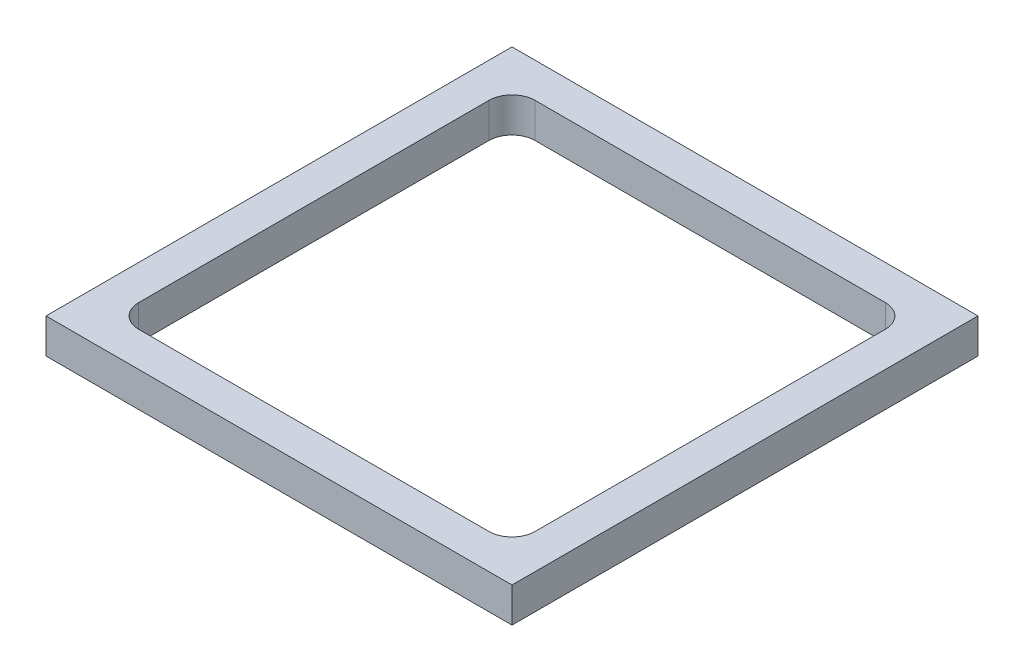
SolidWorks part; units mm, degrees
material "6061-T6 (SS)"
ref_plane "Front Plane" through (0, 0, 0) normal (0, 0, 1) x (1, 0, 0)
ref_plane "Top Plane" through (0, 0, 0) normal (0, 1, 0) x (1, 0, 0)
ref_plane "Right Plane" through (0, 0, 0) normal (1, 0, 0) x (0, 0, -1)
sketch "Sketch1" plane through (0, 0, 0) normal (0, 1, 0) x (1, 0, 0)
  line L5 (0, 0) -> (127.635, 0)
  line L6 (0, 0) -> (0, 127.635)
  line L7 (0, 127.635) -> (127.635, 127.635)
  line L8 (127.635, 0) -> (127.635, 127.635)
  dimension "D1" = 127.635
  dimension "D2" = 127.635
extrude "Boss-Extrude1" add sketch "Sketch1" along normal blind 9.525 contours L5 L8 L7 L6
sketch "Sketch5" plane through (0, 9.525, 0) normal (0, 1, 0) x (1, 0, 0)
  line L0 (63.8175, 127.635) -> (63.8175, 0) construction
  line L1 (0, 127.635) -> (127.635, 127.635) construction
  line L2 (0, 0) -> (127.635, 0) construction
  line L4 (9.525, 118.11) -> (118.11, 118.11)
  line L5 (9.525, 118.11) -> (9.525, 9.525)
  line L6 (9.525, 9.525) -> (118.11, 9.525)
  line L7 (118.11, 118.11) -> (118.11, 9.525)
  line L8 (9.525, 118.11) -> (118.11, 9.525) construction
  line L9 (9.525, 9.525) -> (118.11, 118.11) construction
  point P6 (63.8175, 63.8175)
  dimension "D1" = 108.585
  dimension "D2" = 108.585
extrude "Cut-Extrude1" cut sketch "Sketch5" against normal blind 9.525 contours L5 L4 L7 L6
fillet "Fillet1" radius 6.35 4 edges at (118.11, 4.7625, -9.525) (118.11, 4.7625, -118.11) (9.525, 4.7625, -118.11) (9.525, 4.7625, -9.525)
